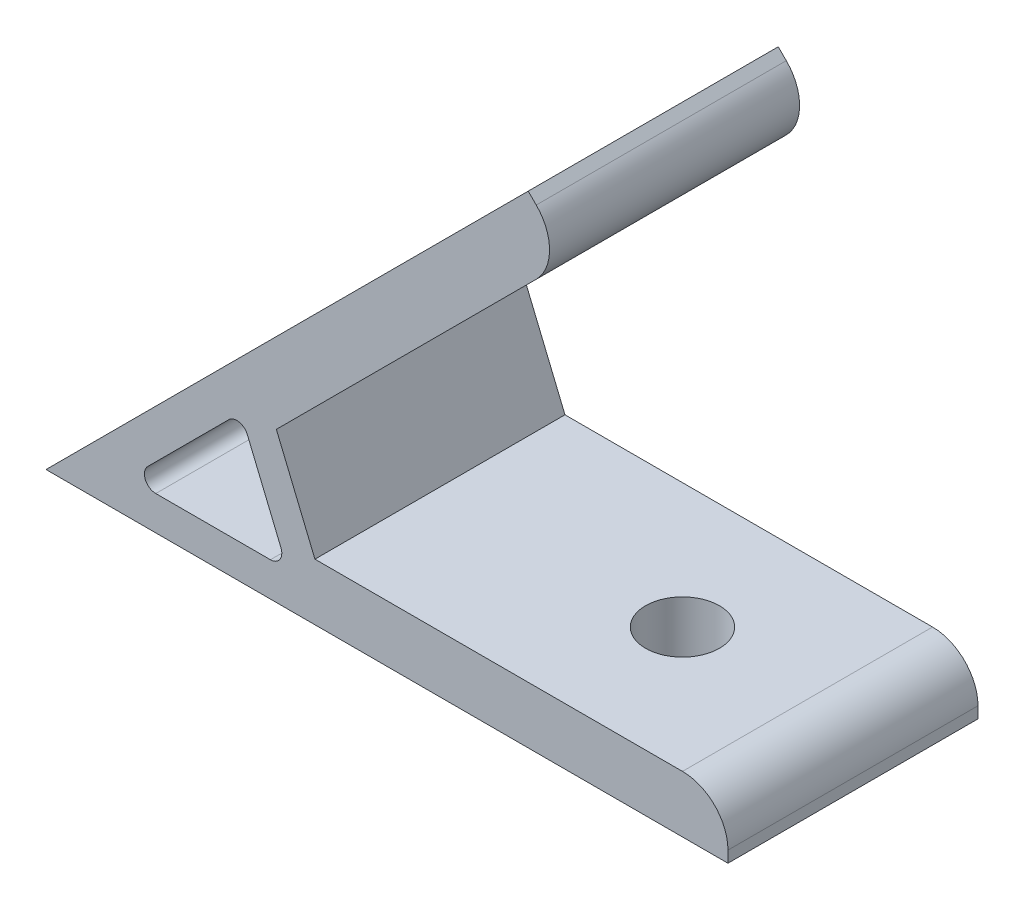
SolidWorks part; units mm, degrees
material "6063 T5"
ref_plane "Спереди" through (0, 0, 0) normal (0, 0, 1) x (1, 0, 0)
ref_plane "Сверху" through (0, 0, 0) normal (0, 1, 0) x (1, 0, 0)
ref_plane "Справа" through (0, 0, 0) normal (1, 0, 0) x (0, 0, -1)
sketch "Эскиз1" plane through (0, 0, 0) normal (0, 0, 1) x (1, 0, 0)
  line L0 (0, 0) -> (42.4264, 42.4264)
  line L1 (42.4264, 42.4264) -> (45.9619, 38.8909)
  line L2 (45.9619, 38.8909) -> (20.2667, 13.1956)
  line L3 (20.2667, 13.1956) -> (23.6614, 5)
  line L4 (23.6614, 5) -> (60, 5)
  line L5 (60, 5) -> (60, 0)
  line L6 (60, 0) -> (0, 0)
  line L7 (17.1421, 12.8995) -> (21.2426, 3)
  line L8 (21.2426, 3) -> (7.2426, 3)
  line L9 (7.2426, 3) -> (17.1421, 12.8995)
  line L10 (14.2426, 3) -> (14.2426, 0) construction
  line L11 (12.1924, 7.9497) -> (10.0711, 10.0711) construction
  line L12 (0, 0) -> (19.1924, 7.9497) construction
  point P15 (39.2751, 39.2751)
  dimension "D1" = 60
  dimension "D2" = 45
  dimension "D3" = 3
  dimension "D4" = 5
  dimension "D5" = 3
  dimension "D6" = 14
extrude "Бобышка-Вытянуть1" add sketch "Эскиз1" along normal mid plane 22
sketch "Эскиз2" plane through (0, 0, 0) normal (-0.7071, 0.7071, 0) x (0, 0, 1)
  line L0 (11, 60) -> (-11, 60) construction
  circle A0 centre (0, 45) radius 3.25
  point P2 (-2.935, 46.7791)
  dimension "D1" = 6.5
  dimension "D2" = 15
extrude "Вырез-Вытянуть1" cut sketch "Эскиз2" against normal up to surface (5 mm away) up to face at (33.1143, 26.0432, 0)
sketch "Эскиз3" plane through (0, 0, 0) normal (0, -1, 0) x (1, 0, 0)
  line L0 (60, 11) -> (60, -11) construction
  circle A0 centre (45, 0) radius 3.25
  point P2 (0, 0)
  dimension "D1" = 6.5
  dimension "D2" = 15
extrude "Вырез-Вытянуть2" cut sketch "Эскиз3" against normal up to surface (5 mm away) up to face at (41.8307, 5, 0)
fillet "Скругление1" radius 4 2 edges at (60, 5, 0) (45.9619, 38.8909, 0)
fillet "Скругление2" radius 1 3 edges at (17.1421, 12.8995, 0) (7.2426, 3, 0) (21.2426, 3, 0)
